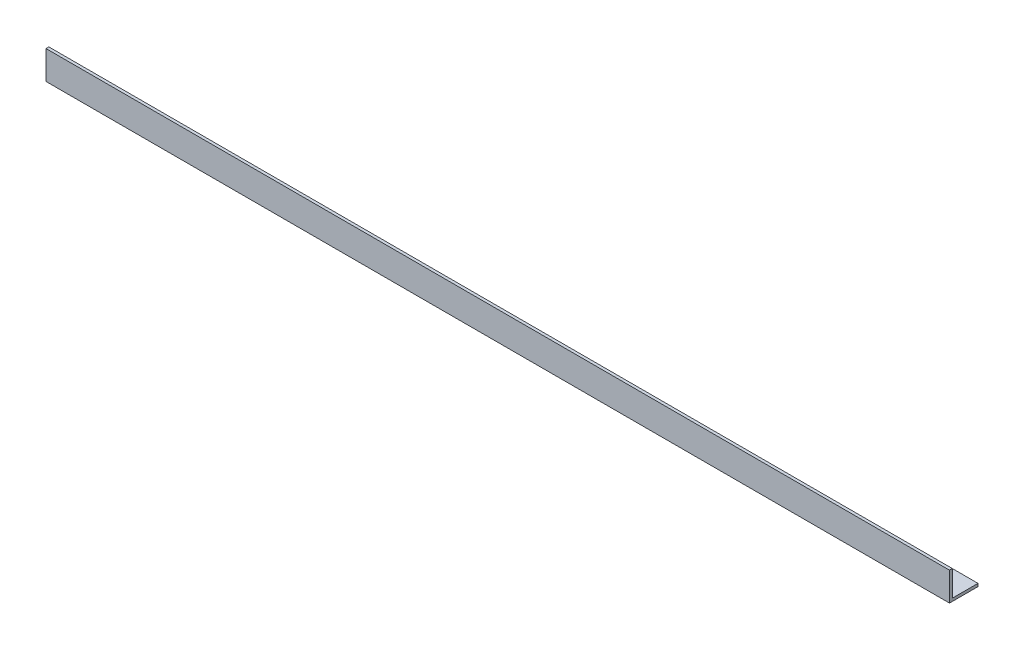
SolidWorks part; units mm, degrees
ref_plane "Спереди" through (0, 0, 0) normal (0, 0, 1) x (1, 0, 0)
ref_plane "Сверху" through (0, 0, 0) normal (0, 1, 0) x (1, 0, 0)
ref_plane "Справа" through (0, 0, 0) normal (1, 0, 0) x (0, 0, -1)
sketch "Эскиз1" plane through (0, 0, 0) normal (1, 0, 0) x (0, 0, -1)
  line L0 (0, 0) -> (0, 15)
  line L1 (0, 15) -> (1.5, 15)
  line L2 (1.5, 15) -> (1.5, 1.5)
  line L3 (1.5, 1.5) -> (15, 1.5)
  line L4 (15, 1.5) -> (15, 0)
  line L5 (15, 0) -> (0, 0)
  dimension "D1" = 15
  dimension "D2" = 15
  dimension "D3" = 1.5
  dimension "D4" = 1.5
extrude "Бобышка-Вытянуть1" add sketch "Эскиз1" along normal blind 475
